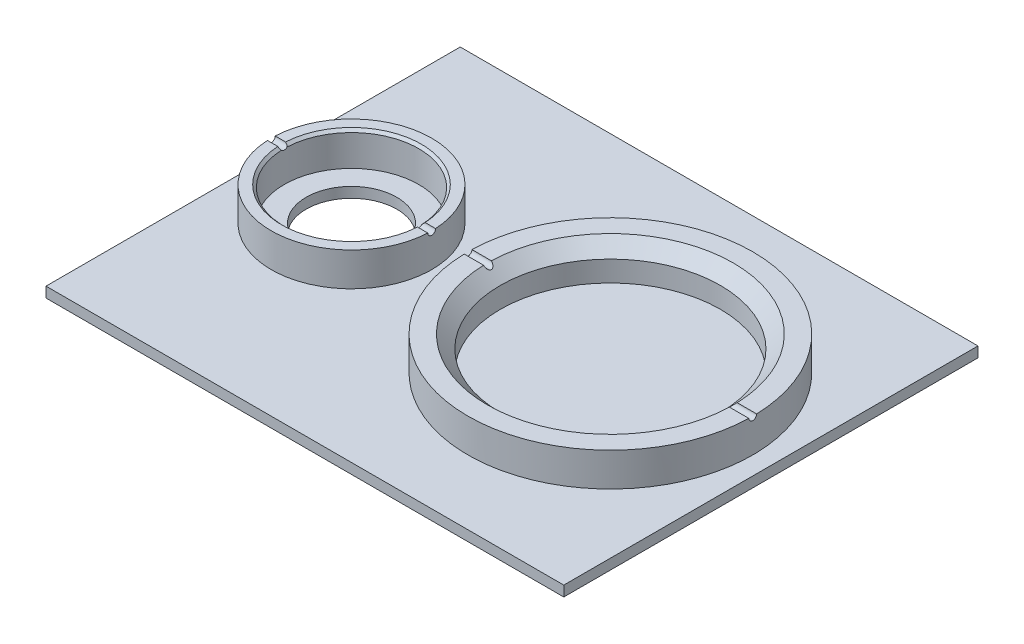
SolidWorks part; units mm, degrees
other "Markup1" [suppressed]
sketch "Sketch8" [suppressed] plane through (-100, 19, -80) normal (-0.5477, 0.8146, -0.1911) x (0.8292, 0.5589, 0.0062)
material "Plain Carbon Steel"
ref_plane "Front Plane" through (0, 0, 0) normal (0, 0, 1) x (1, 0, 0)
ref_plane "Top Plane" through (0, 0, 0) normal (0, 1, 0) x (1, 0, 0)
ref_plane "Right Plane" through (0, 0, 0) normal (1, 0, 0) x (0, 0, -1)
sketch "Sketch1" plane through (0, 0, 0) normal (0, 1, 0) x (1, 0, 0)
  line L1 (-100, -80) -> (100, -80)
  line L2 (-100, -80) -> (-100, 80)
  line L3 (-100, 80) -> (100, 80)
  line L4 (100, -80) -> (100, 80)
  line L5 (-100, -80) -> (100, 80) construction
  line L6 (-100, 80) -> (100, -80) construction
  point P0 (0, 0)
  dimension "D1" = 160
  dimension "D2" = 200
extrude "Boss-Extrude1" add sketch "Sketch1" along normal blind 4
sketch "Sketch2" plane through (0, 4, 0) normal (0, 1, 0) x (1, 0, 0)
  line L0 (-100, 80) -> (-100, -80) construction
  circle A0 centre (-62, 0) radius 31
  circle A1 centre (38, 0) radius 55
  circle A2 centre (-62, 0) radius 26
  circle A3 centre (38, 0) radius 42.5
  dimension "D1" = 110
  dimension "D2" = 62
  dimension "D5" = 85
  dimension "D6" = 52
  dimension "D3" = 100
  dimension "D4" = 38
extrude "Boss-Extrude2" add sketch "Sketch2" along normal blind 13
chamfer "Chamfer2" distance 5 angle 45 1 edges at (38, 17, 42.5)
chamfer "Chamfer3" [suppressed] distance 1 angle 45
sketch "Sketch4" plane through (0, 4, 0) normal (0, 1, 0) x (1, 0, 0)
  circle A1 centre (38, 0) radius 32.5
  dimension "D2" = 65
extrude "Cut-Extrude4" [suppressed] cut sketch "Sketch4" against normal through all
sketch "Sketch6" [suppressed] plane through (0, 0, 0) normal (0, -1, 0) x (1, 0, 0)
  line L0 (-100, 75) -> (100, 75) construction
  line L1 (100, 80) -> (100, -80) construction
  line L2 (0, 80) -> (0, -80) construction
  line L3 (-100, 80) -> (100, 80) construction
  line L4 (100, -80) -> (-100, -80) construction
  line L5 (100, 0) -> (-100, 0) construction
  line L6 (-100, -80) -> (-100, 80) construction
  circle A0 centre (87, 62) radius 6.5
  circle A1 centre (-87, 62) radius 6.5
  circle A2 centre (-87, -62) radius 6.5
  circle A3 centre (87, -62) radius 6.5
  circle A4 centre (0, 62) radius 6.5
  circle A5 centre (0, -62) radius 6.5
  circle A6 centre (67, 62) radius 3
  circle A7 centre (-67, -62) radius 3
  dimension "D1" = 13
  dimension "D4" = 13
  dimension "D5" = 13
  dimension "D6" = 6
  dimension "D7" = 6
  dimension "D2" = 13
  dimension "D3" = 13
  dimension "D8" = 20
  dimension "D9" = 20
extrude "Cut-Extrude6" [suppressed] cut sketch "Sketch6" against normal through all
sketch "Sketch7" [suppressed] plane through (0, 4, 0) normal (0, 1, 0) x (1, 0, 0)
  line L0 (-100, 0) -> (100, 0) construction
  line L1 (-100, 80) -> (-100, -80) construction
  line L2 (100, -80) -> (100, 80) construction
  circle A0 centre (-87, 62) radius 6.5
  circle A1 centre (0, 62) radius 6.5
  circle A2 centre (87, 62) radius 6.5
  circle A3 centre (87, -62) radius 6.5
  circle A4 centre (0, -62) radius 6.5
  circle A5 centre (-87, -62) radius 6.5
  circle A6 centre (-67, -62) radius 3
  circle A7 centre (67, 62) radius 3
  dimension "D1" = 13
  dimension "D2" = 13
  dimension "D3" = 13
  dimension "D4" = 6
  dimension "D5" = 6
extrude "Cut-Extrude7" [suppressed] cut sketch "Sketch7" against normal through all
chamfer "Chamfer4" distance 1 angle 45 1 edges at (-62, 17, 26)
sketch "Sketch9" plane through (0, 4, 0) normal (0, 1, 0) x (1, 0, 0)
  circle A0 centre (-62, 0) radius 17.5
  dimension "D1" = 35
extrude "Cut-Extrude8" cut sketch "Sketch9" against normal through all
chamfer "Chamfer5" [suppressed] distance 1 angle 45
sketch "Sketch10" [suppressed] plane through (0, 0, 0) normal (1, 0, 0) x (0, 0, -1)
  line L0 (31, 17) -> (-31, 17) construction
  circle A0 centre (0, 17) radius 1.5
  dimension "D1" = 3
extrude "Cut-Extrude9" [suppressed] cut sketch "Sketch10" against normal through all both and the other way through all
sketch "Sketch11" plane through (0, 0, 0) normal (1, 0, 0) x (0, 0, -1)
  line L0 (31, 17) -> (-31, 17) construction
  circle A0 centre (0, 17) radius 1.5
extrude "Cut-Extrude10" cut sketch "Sketch11" against normal through all both and the other way through all
